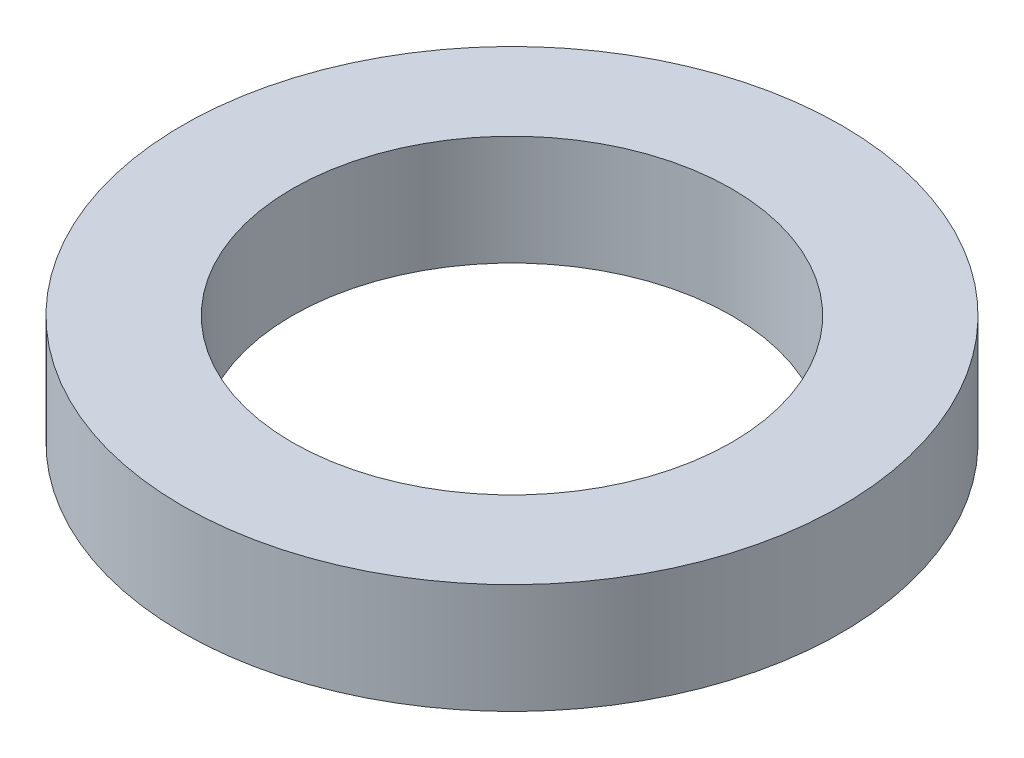
SolidWorks part; units mm, degrees
material "Plain Carbon Steel"
ref_plane "Front Plane" through (0, 0, 0) normal (0, 0, 1) x (1, 0, 0)
ref_plane "Top Plane" through (0, 0, 0) normal (0, 1, 0) x (1, 0, 0)
ref_plane "Right Plane" through (0, 0, 0) normal (1, 0, 0) x (0, 0, -1)
sketch "Sketch1" plane through (0, 0, 0) normal (0, 1, 0) x (1, 0, 0)
  circle A0 centre (0, 0) radius 12.7
  circle A1 centre (0, 0) radius 19.05
  dimension "D1" = 25.4
  dimension "D2" = 38.1
extrude "Boss-Extrude1" add sketch "Sketch1" along normal blind 6.35
